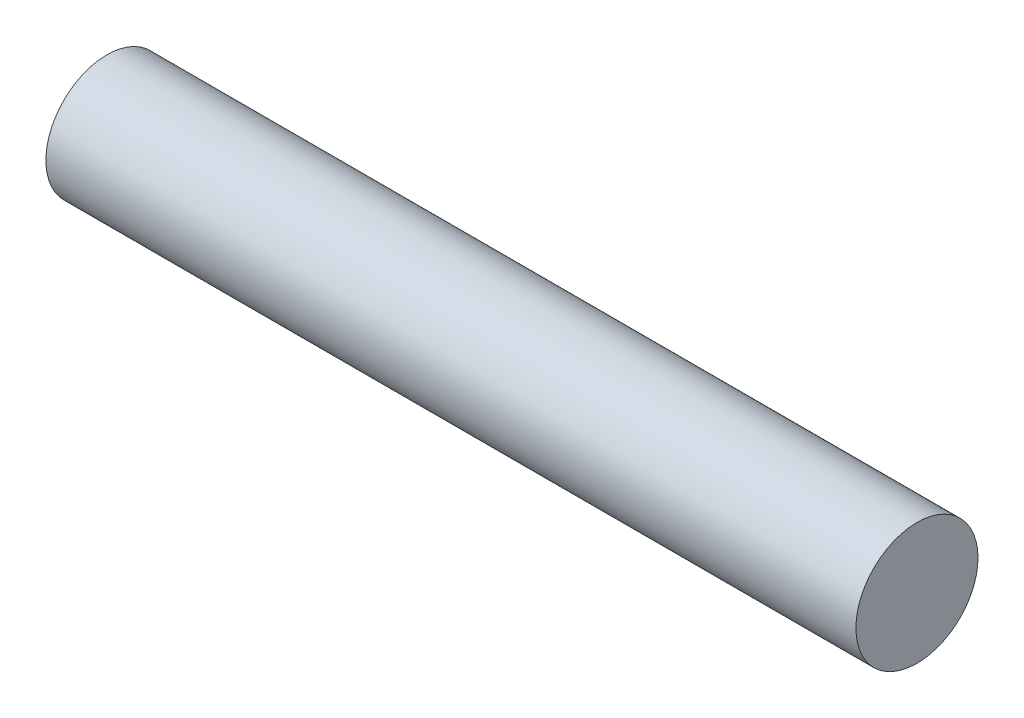
SolidWorks part; units mm, degrees
ref_plane "Front Plane" through (0, 0, 0) normal (0, 0, 1) x (1, 0, 0)
ref_plane "Top Plane" through (0, 0, 0) normal (0, 1, 0) x (1, 0, 0)
ref_plane "Right Plane" through (0, 0, 0) normal (1, 0, 0) x (0, 0, -1)
sketch "Sketch1" plane through (0, 0, 0) normal (1, 0, 0) x (0, 0, -1)
  circle A0 centre (0, 0) radius 7
  dimension "D1" = 14
extrude "Boss-Extrude1" add sketch "Sketch1" along normal blind 92.9
